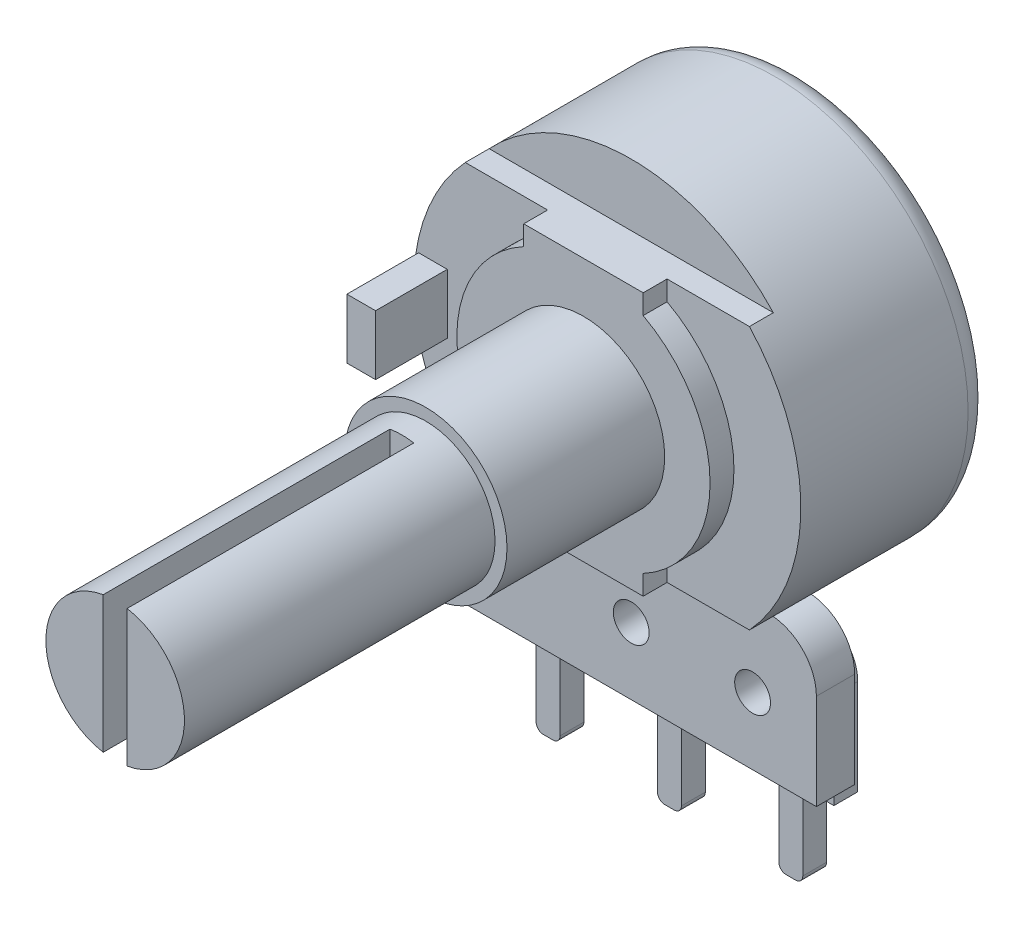
SolidWorks part; units mm, degrees
ref_plane "Ön Düzlem" through (0, 0, 0) normal (0, 0, 1) x (1, 0, 0)
ref_plane "Üst Düzlem" through (0, 0, 0) normal (0, 1, 0) x (1, 0, 0)
ref_plane "Sağ Düzlem" through (0, 0, 0) normal (1, 0, 0) x (0, 0, -1)
sketch "Çizim1" plane through (0, 0, 0) normal (0, 0, 1) x (1, 0, 0)
  circle A0 centre (0, 0) radius 8.1
  dimension "D1" = 16.2
extrude "Yükseklik-Ekstrüzyon1" add sketch "Çizim1" along normal blind 7
fillet "Radyus1" radius 1 1 edges at (8.1, 0, 0)
sketch "Çizim2" plane through (0, 0, 7) normal (0, 0, 1) x (1, 0, 0)
  line L1 (-5.9464, 5.5) -> (5.9464, 5.5)
  line L3 (-5.9464, -5.5) -> (5.9464, -5.5)
  arc A0 (-5.9464, 5.5) -> (-5.9464, -5.5) centre (0, 0) ccw
  arc A1 (5.9464, -5.5) -> (5.9464, 5.5) centre (0, 0) ccw
  dimension "D1" = 5.5
extrude "Yükseklik-Ekstrüzyon2" add sketch "Çizim2" along normal blind 1
sketch "Çizim3" plane through (0, 0, 8) normal (0, 0, 1) x (1, 0, 0)
  line L0 (-2.5, 5.5) -> (2.5, 5.5)
  line L2 (-2.5, 5.5) -> (-2.5, 4.6733)
  line L3 (-2.5, -4.6733) -> (-2.5, -5.5)
  line L4 (2.5, 5.5) -> (2.5, 4.6733)
  line L6 (-2.5, -5.5) -> (2.5, -5.5)
  line L8 (2.5, -4.6733) -> (2.5, -5.5)
  arc A0 (2.5, -4.6733) -> (2.5, 4.6733) centre (0, 0) ccw
  arc A1 (-2.5, 4.6733) -> (-2.5, -4.6733) centre (0, 0) ccw
  dimension "D1" = 10.6
  dimension "D2" = 2.5
extrude "Yükseklik-Ekstrüzyon3" add sketch "Çizim3" along normal blind 1
sketch "Çizim4" plane through (0, 0, 8) normal (0, 0, 1) x (1, 0, 0)
  line L1 (-7.9, 1.25) -> (-6.7, 1.25)
  line L2 (-7.9, 1.25) -> (-7.9, -1.25)
  line L3 (-7.9, -1.25) -> (-6.7, -1.25)
  line L4 (-6.7, 1.25) -> (-6.7, -1.25)
  dimension "D1" = 2.5
  dimension "D2" = 1.2
  dimension "D3" = 1.25
  dimension "D4" = 7.9
extrude "Yükseklik-Ekstrüzyon4" add sketch "Çizim4" along normal blind 3
sketch "Çizim5" plane through (0, 0, 9) normal (0, 0, 1) x (1, 0, 0)
  circle A0 centre (0, 0) radius 3.4
  dimension "D1" = 6.8
extrude "Yükseklik-Ekstrüzyon5" add sketch "Çizim5" along normal blind 6.6
sketch "Çizim6" plane through (0, 0, 15.6) normal (0, 0, 1) x (1, 0, 0)
  circle A0 centre (0, 0) radius 2.9
  dimension "D1" = 5.8
extrude "Yükseklik-Ekstrüzyon6" add sketch "Çizim6" along normal blind 1
sketch "Çizim7" plane through (0, 0, 16.6) normal (0, 0, 1) x (1, 0, 0)
  line L2 (-0.5, 2.8566) -> (-0.5, -2.8566)
  line L4 (0.5, 2.8566) -> (0.5, -2.8566)
  arc A0 (0.5, -2.8566) -> (0.5, 2.8566) centre (0, 0) ccw
  arc A1 (-0.5, 2.8566) -> (-0.5, -2.8566) centre (0, 0) ccw
  dimension "D1" = 0.5
extrude "Yükseklik-Ekstrüzyon7" add sketch "Çizim7" along normal blind 12
sketch "Çizim8" plane through (0, 0, 7) normal (0, 0, 1) x (1, 0, 0)
  line L1 (-5.9464, -5.5) -> (7.7559, -5.5)
  line L2 (-5.9464, -5.5) -> (-5.9464, -10.0353)
  line L3 (-5.9464, -10.0353) -> (7.7559, -10.0353)
  line L4 (7.7559, -5.5) -> (7.7559, -10.0353)
extrude "Kes-Ekstrüzyon1" cut sketch "Çizim8" against normal blind 3.5
sketch "Çizim9" plane through (0, 0, 3.5) normal (0, 0, 1) x (1, 0, 0)
  line L0 (-7.75, -11.5) -> (7.75, -11.5)
  line L1 (5.9464, -5.5) -> (-5.9464, -5.5) construction
  line L2 (-5.75, -5.5) -> (5.75, -5.5)
  line L6 (-7.75, -11.5) -> (-7.75, -7.5)
  line L8 (7.75, -11.5) -> (7.75, -7.5)
  arc A0 (5.75, -5.5) -> (7.75, -7.5) centre (5.75, -7.5) cw
  arc A1 (-5.75, -5.5) -> (-7.75, -7.5) centre (-5.75, -7.5) ccw
  circle A2 centre (0, -8.7) radius 0.75
  circle A3 centre (5.08, -8.7) radius 0.75
  circle A4 centre (-5.08, -8.7) radius 0.75
  dimension "D4" = 2
  dimension "D5" = 1.5
  dimension "D1" = 15.5
  dimension "D2" = 7.75
  dimension "D3" = 6
  dimension "D6" = 2.8
extrude "Yükseklik-Ekstrüzyon8" add sketch "Çizim9" along normal blind 1.6 from offset 1.9
sketch "Çizim10" plane through (0, 0, 5.4) normal (0, 0, -1) x (-1, 0, 0)
  line L0 (3.53, -12.7) -> (4.58, -12)
  line L1 (-1.55, -12.7) -> (-0.5, -12)
  line L2 (3.28, -8.7) -> (3.28, -12.7)
  line L3 (3.28, -12.7) -> (3.53, -12.7)
  line L4 (6.88, -8.7) -> (6.88, -12.7)
  line L5 (4.58, -12) -> (4.58, -15.9)
  line L6 (4.88, -16.2) -> (5.28, -16.2)
  line L7 (5.58, -12) -> (5.58, -15.9)
  line L8 (-1.8, -8.7) -> (-1.8, -12.7)
  line L9 (6.63, -12.7) -> (5.58, -12)
  line L10 (-1.8, -12.7) -> (-1.55, -12.7)
  line L11 (6.63, -12.7) -> (6.88, -12.7)
  line L12 (1.8, -8.7) -> (1.8, -12.7)
  line L13 (-0.5, -12) -> (-0.5, -15.9)
  line L14 (-0.2, -16.2) -> (0.2, -16.2)
  line L15 (0.5, -12) -> (0.5, -15.9)
  line L16 (1.55, -12.7) -> (0.5, -12)
  line L17 (1.55, -12.7) -> (1.8, -12.7)
  line L18 (-6.63, -12.7) -> (-5.58, -12)
  line L19 (-6.88, -8.7) -> (-6.88, -12.7)
  line L20 (-6.88, -12.7) -> (-6.63, -12.7)
  line L21 (-3.28, -8.7) -> (-3.28, -12.7)
  line L22 (-5.58, -12) -> (-5.58, -15.9)
  line L23 (-5.28, -16.2) -> (-4.88, -16.2)
  line L24 (-4.58, -12) -> (-4.58, -15.9)
  line L25 (-3.53, -12.7) -> (-4.58, -12)
  line L26 (-3.53, -12.7) -> (-3.28, -12.7)
  arc A0 (6.88, -8.7) -> (3.28, -8.7) centre (5.08, -8.7) ccw
  arc A1 (5.28, -16.2) -> (5.58, -15.9) centre (5.28, -15.9) ccw
  arc A2 (4.58, -15.9) -> (4.88, -16.2) centre (4.88, -15.9) ccw
  arc A3 (1.8, -8.7) -> (-1.8, -8.7) centre (0, -8.7) ccw
  arc A4 (0.2, -16.2) -> (0.5, -15.9) centre (0.2, -15.9) ccw
  arc A5 (-0.5, -15.9) -> (-0.2, -16.2) centre (-0.2, -15.9) ccw
  arc A6 (-3.28, -8.7) -> (-6.88, -8.7) centre (-5.08, -8.7) ccw
  arc A7 (-4.88, -16.2) -> (-4.58, -15.9) centre (-4.88, -15.9) ccw
  arc A8 (-5.58, -15.9) -> (-5.28, -16.2) centre (-5.28, -15.9) ccw
  point P12 (5.58, -16.2)
  point P17 (4.58, -16.2)
  dimension "D1" = 3.6
  dimension "D8" = 0.3
  dimension "D2" = 4
  dimension "D3" = 3.5
  dimension "D4" = 1
  dimension "D5" = 0.5
  dimension "D6" = 0.25
  dimension "D7" = 0.7
extrude "Yükseklik-Ekstrüzyon9" add sketch "Çizim10" along normal blind 1
